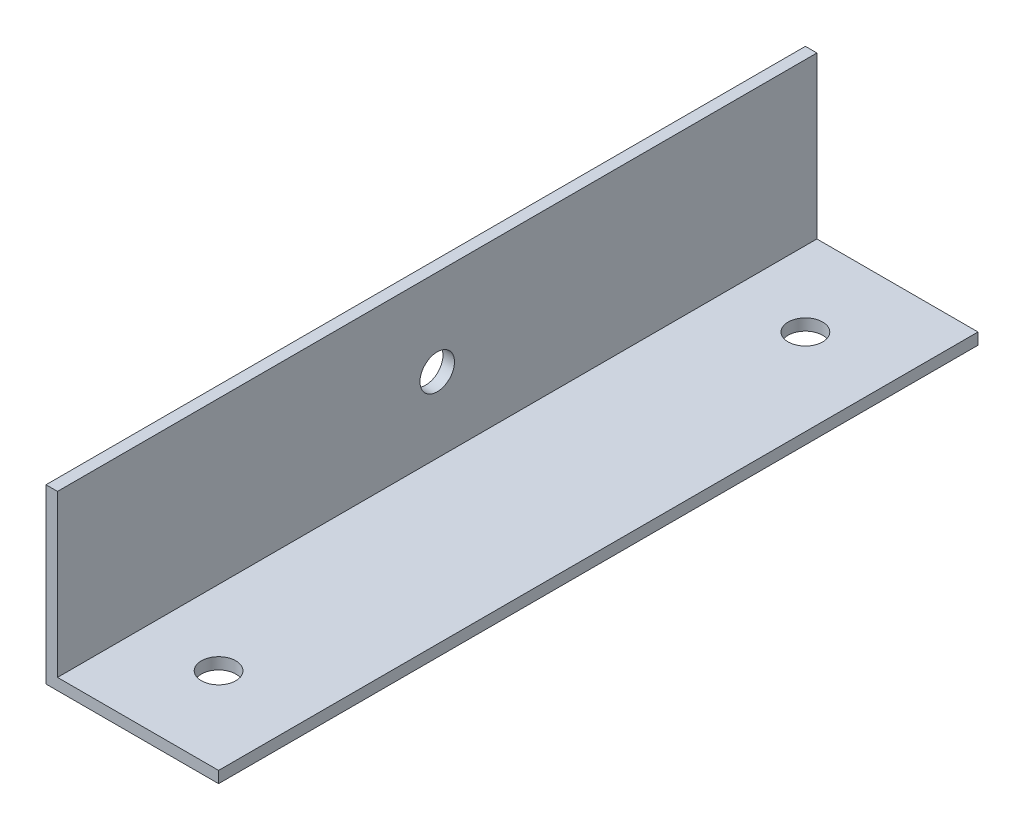
SolidWorks part; units mm, degrees
material "1060 合金"
ref_plane "正面" through (0, 0, 0) normal (0, 0, 1) x (1, 0, 0)
ref_plane "平面" through (0, 0, 0) normal (0, 1, 0) x (1, 0, 0)
ref_plane "右側面" through (0, 0, 0) normal (1, 0, 0) x (0, 0, -1)
sketch "ｽｹｯﾁ1" plane through (0, 0, 0) normal (0, 0, 1) x (1, 0, 0)
  line L1 (-5.4615, 6.3533) -> (9.5385, 6.3533)
  line L2 (-5.4615, 6.3533) -> (-5.4615, -8.6467)
  line L3 (-5.4615, -8.6467) -> (9.5385, -8.6467)
  line L4 (9.5385, 6.3533) -> (9.5385, -8.6467)
  line L5 (9.5385, 6.3533) -> (-4.4615, 6.3533)
  line L6 (9.5385, 6.3533) -> (9.5385, -7.6467)
  line L7 (9.5385, -7.6467) -> (-4.4615, -7.6467)
  line L8 (-4.4615, 6.3533) -> (-4.4615, -7.6467)
  dimension "D1" = 15
  dimension "D2" = 15
  dimension "D3" = 1
  dimension "D4" = 1
extrude "ﾎﾞｽ - 押し出し1" add sketch "ｽｹｯﾁ1" along normal blind 66 contours L8 L1 L2 L3 L4 L7
sketch "ｽｹｯﾁ3" plane through (-4.4615, 0, 0) normal (1, 0, 0) x (0, 0, -1)
  line L1 (-66, 6.3533) -> (0, 6.3533) construction
  circle A1 centre (-33, -1.1467) radius 1.5
  point P4 (-33, 6.3533)
  dimension "D1" = 7.5
extrude "ｶｯﾄ - 押し出し1" cut sketch "ｽｹｯﾁ3" against normal blind 10
sketch "ｽｹｯﾁ4" plane through (0, -7.6467, 0) normal (0, 1, 0) x (1, 0, 0)
  line L0 (9.5385, -66) -> (9.5385, 0) construction
  line L1 (9.5385, 0) -> (-4.4615, 0) construction
  circle A0 centre (2.0385, -7.5) radius 1.5
  point P2 (-8.6471, 9.5499)
  dimension "D1" = 3
  dimension "D2" = 7.5
  dimension "D3" = 7.5
extrude "ｶｯﾄ - 押し出し2" cut sketch "ｽｹｯﾁ4" against normal blind 10
sketch "ｽｹｯﾁ5" plane through (0, -7.6467, 0) normal (0, 1, 0) x (1, 0, 0)
  line L0 (9.5385, -66) -> (-4.4615, -66) construction
  line L1 (9.5385, -66) -> (9.5385, 0) construction
  circle A0 centre (2.0385, -58.5) radius 1.5
  dimension "D1" = 7.5
  dimension "D2" = 7.5
extrude "ｶｯﾄ - 押し出し3" cut sketch "ｽｹｯﾁ5" against normal blind 10
